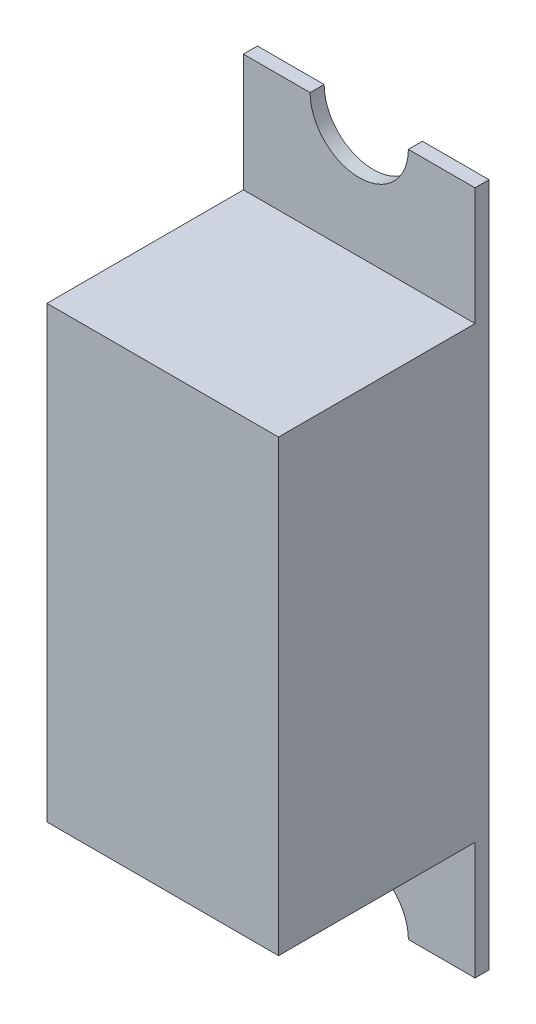
SolidWorks part; units mm, degrees
ref_plane "Plan de face" through (0, 0, 0) normal (0, 0, 1) x (1, 0, 0)
ref_plane "Plan de dessus" through (0, 0, 0) normal (0, 1, 0) x (1, 0, 0)
ref_plane "Plan de droite" through (0, 0, 0) normal (1, 0, 0) x (0, 0, -1)
sketch "Esquisse1" plane through (0, 0, 0) normal (0, 0, 1) x (1, 0, 0)
  line L1 (0, 0) -> (-6.6, 0)
  line L2 (0, 0) -> (0, -12.8)
  line L3 (0, -12.8) -> (-6.6, -12.8)
  line L4 (-6.6, 0) -> (-6.6, -12.8)
  line L7 (-3.3, 0) -> (-3.3, -12.8) construction
  point P6 (-3.3, -6.4)
  point P8 (17.3651, -7.1445)
  dimension "D1" = 12.8
  dimension "D2" = 6.6
extrude "Boss.-Extru.1" add sketch "Esquisse1" along normal blind 5.6
sketch "Esquisse2" plane through (0, 0, 0) normal (0, 0, -1) x (-1, 0, 0)
  line L0 (6.6, 0) -> (6.6, -12.8) construction
  line L1 (0, 3.35) -> (6.6, 3.35)
  line L2 (0, 3.35) -> (0, -16.15)
  line L3 (0, -16.15) -> (6.6, -16.15)
  line L4 (6.6, 3.35) -> (6.6, -16.15)
  line L5 (0, -12.8) -> (0, 0) construction
  line L7 (6.6, -12.8) -> (0, -12.8) construction
  line L9 (0, 0) -> (6.6, 0) construction
  line L11 (1.9, 3.35) -> (4.7, 3.35)
  line L12 (1.9, 3.35) -> (1.9, -16.15)
  line L13 (1.9, -16.15) -> (4.7, -16.15)
  line L14 (4.7, 3.35) -> (4.7, -16.15)
  arc A0 (1.9, 3.35) -> (4.7, 3.35) centre (3.3, 3.35) ccw
  arc A1 (1.9, -16.15) -> (4.7, -16.15) centre (3.3, -16.15) cw
  point P16 (3.3, 3.35)
  line M5 (0, 0) -> (0, -12.8)
  line M6 (0, -12.8) -> (6.6, -12.8)
  line M7 (6.6, -12.8) -> (6.6, 0)
  line M8 (6.6, 0) -> (0, 0)
  dimension "D1" = 0
  dimension "D2" = 0
  dimension "D3" = 19.5
  dimension "D4" = 3.35
  dimension "D5" = 3.35
  dimension "D6" = 2.8
  dimension "D7" = 1.4
extrude "Boss.-Extru.2" add sketch "Esquisse2" along normal blind 0.4 contours L12 M8 M5 M6 | L14 L12 M8 M6 | L14 M8 M6 M7 | L12 L2 L3 M6 | L12 A1 L14 M6 | L14 L3 L4 M6 | L12 L1 L2 M8 | A0 L12 L14 M8 | L1 L14 L4 M8
